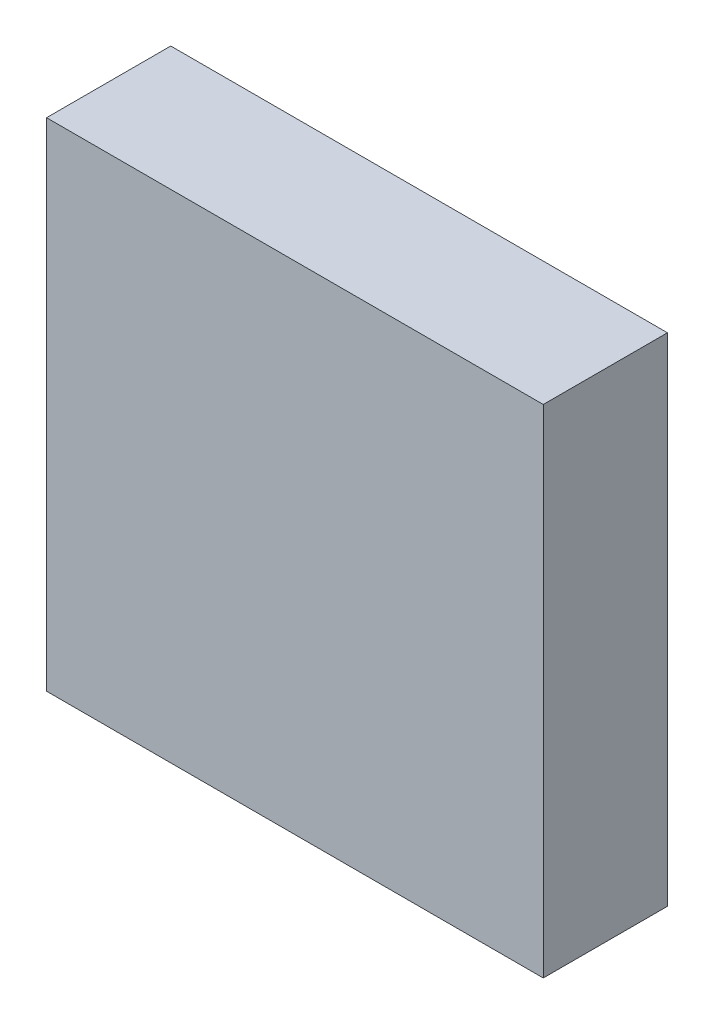
SolidWorks part; units mm, degrees
ref_plane "Plan de face" through (0, 0, 0) normal (0, 0, 1) x (1, 0, 0)
ref_plane "Plan de dessus" through (0, 0, 0) normal (0, 1, 0) x (1, 0, 0)
ref_plane "Plan de droite" through (0, 0, 0) normal (1, 0, 0) x (0, 0, -1)
sketch "Esquisse3" plane through (0, 0, 0) normal (0, 0, 1) x (1, 0, 0)
  line L1 (0, 0) -> (120, 0)
  line L2 (0, 0) -> (0, 120)
  line L3 (0, 120) -> (120, 120)
  line L4 (120, 0) -> (120, 120)
  dimension "D1" = 120
  dimension "D2" = 120
extrude "Boss.-Extru.1" add sketch "Esquisse3" along normal blind 30
